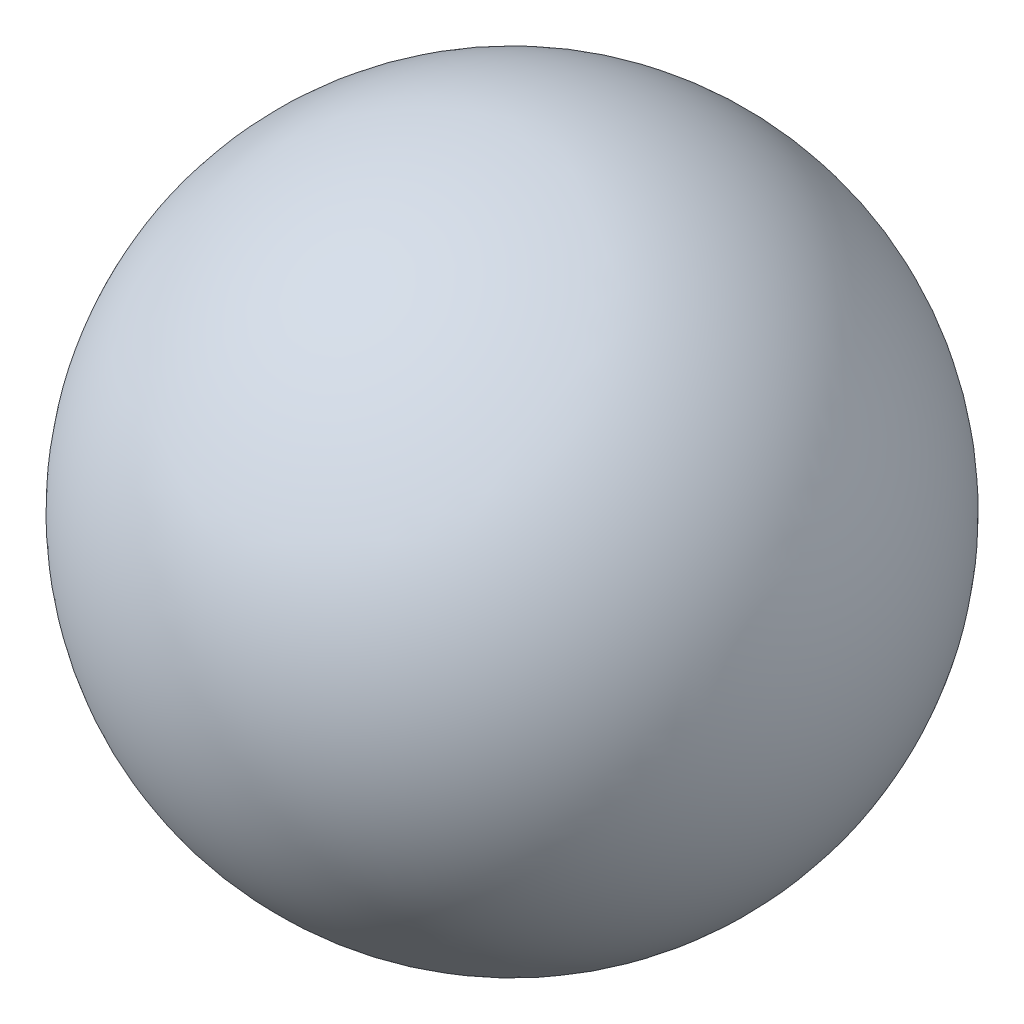
SolidWorks part; units mm, degrees
ref_plane "Plano frontal" through (0, 0, 0) normal (0, 0, 1) x (1, 0, 0)
ref_plane "Plano superior" through (0, 0, 0) normal (0, 1, 0) x (1, 0, 0)
ref_plane "Plano direito" through (0, 0, 0) normal (1, 0, 0) x (0, 0, -1)
sketch "Esboço2" plane through (0, 0, 0) normal (0, 0, 1) x (1, 0, 0)
  line L0 (25, 0) -> (-25, 0)
  arc A0 (25, 0) -> (-25, 0) centre (0, 0) ccw
  dimension "D1" = 50
revolve "Revolução1" add sketch "Esboço2" angle 360 about L0
